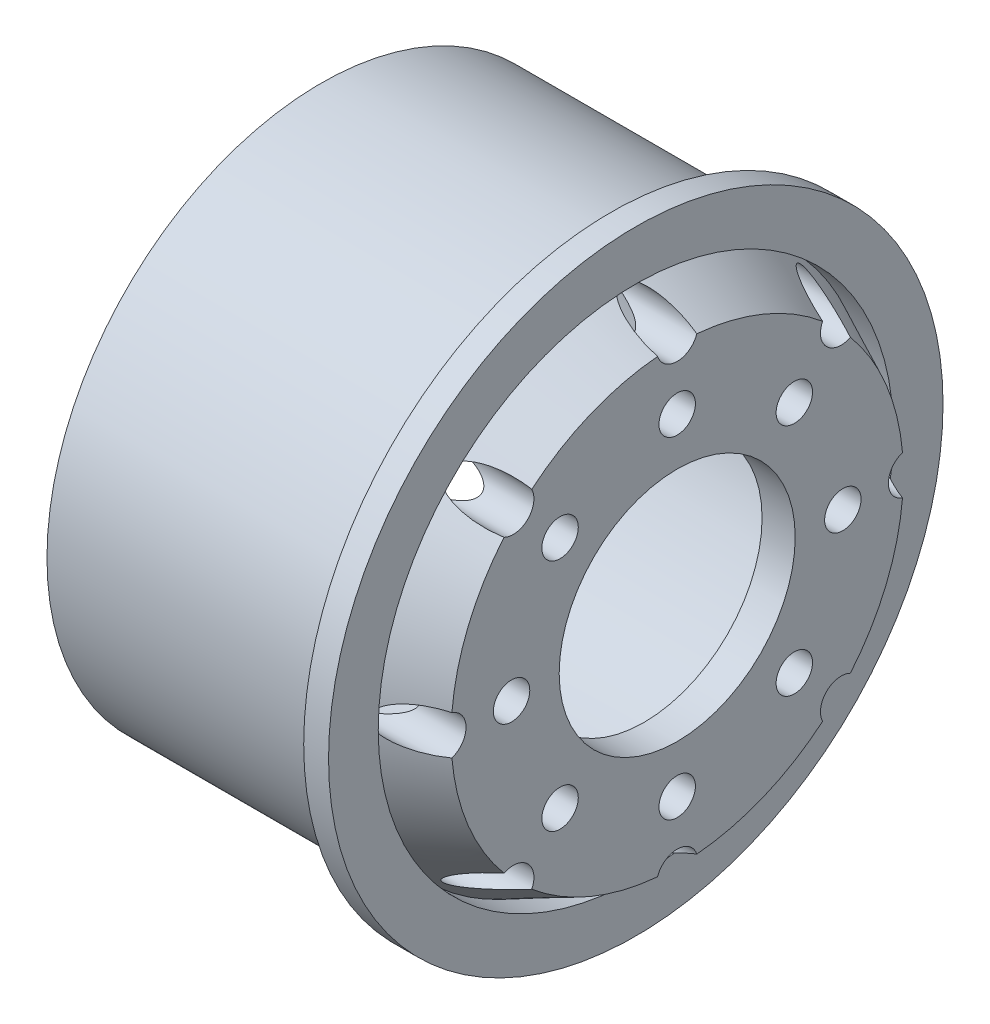
SolidWorks part; units mm, degrees
ref_plane "Front Plane" through (0, 0, 0) normal (0, 0, 1) x (1, 0, 0)
ref_plane "Top Plane" through (0, 0, 0) normal (0, 1, 0) x (1, 0, 0)
ref_plane "Right Plane" through (0, 0, 0) normal (1, 0, 0) x (0, 0, -1)
sketch "Sketch1" plane through (0, 0, 0) normal (0, 1, 0) x (1, 0, 0)
  line L0 (-37.2789, 0) -> (44.8184, 0) construction
  line L7 (8.9363, 7.125) -> (8.9363, 13.6543)
  line L11 (-12.5637, 14.55) -> (4.1816, 13.6944)
  line L12 (-12.5637, 14.55) -> (-12.5637, 16.55)
  line L13 (-12.5637, 16.55) -> (4.9363, 16.55)
  line L14 (6.4363, 16.55) -> (6.4363, 15.55)
  line L15 (6.4363, 16.55) -> (6.4363, 18.55)
  line L16 (6.4363, 18.55) -> (4.9363, 18.55)
  line L17 (4.9363, 18.55) -> (4.9363, 16.55)
  line L18 (6.4363, 15.55) -> (4.9363, 15.55)
  line L21 (6.9363, 12.3889) -> (6.9363, 7.125)
  line L22 (6.9363, 7.125) -> (8.9363, 7.125)
  line L23 (4.9363, 15.55) -> (8.9363, 13.6543)
  line L24 (4.1816, 13.6944) -> (6.9363, 12.3889)
  line L28 (4.0798, 13.7427) -> (8.0798, 11.847) construction
  point P4 (7.9363, 16.8502)
  dimension "D1" = 29.1
  dimension "D2" = 5.2639
  dimension "D4" = 2
  dimension "D5" = 16.7453
  dimension "D6" = 19
  dimension "D7" = 1.5
  dimension "D8" = 2
  dimension "D9" = 1.5
  dimension "D10" = 1
  dimension "D11" = 14.25
  dimension "D12" = 33.1
  dimension "D3" = 2
  dimension "D13" = 2.5
  dimension "D15" = 19.5
  dimension "D16" = 3.0484
  dimension "D17" = 27.3888
  dimension "D18" = 2.7547
  dimension "D19" = 24.7779
  dimension "D20" = 27.3888
  dimension "D21" = 1.3055
  dimension "D14" = 2
revolve "Revolve1" add sketch "Sketch1" angle 360 about L0
sketch "Sketch2" plane through (8.9363, 0, 0) normal (1, 0, 0) x (0, 0, -1)
  line L0 (0, 13.6543) -> (0, -13.6543) construction
  line L1 (-13.6543, 0) -> (13.6543, 0) construction
  circle A0 centre (0, 0) radius 13.6543 construction
  circle A1 centre (0, 0) radius 10 construction
  circle A2 centre (0, 10) radius 1.1
  circle A3 centre (7.0711, 7.0711) radius 1.1
  circle A4 centre (10, 0) radius 1.1
  circle A5 centre (7.0711, -7.0711) radius 1.1
  circle A6 centre (0, -10) radius 1.1
  circle A7 centre (-7.0711, -7.0711) radius 1.1
  circle A8 centre (-10, 0) radius 1.1
  circle A9 centre (-7.0711, 7.0711) radius 1.1
  circle A12 centre (0, 0) radius 14 construction
  circle A13 centre (0, -14) radius 1.25
  circle A14 centre (-9.8995, -9.8995) radius 1.25
  circle A15 centre (-14, 0) radius 1.25
  circle A16 centre (-9.8995, 9.8995) radius 1.25
  circle A17 centre (0, 14) radius 1.25
  circle A18 centre (9.8995, 9.8995) radius 1.25
  circle A19 centre (14, 0) radius 1.25
  circle A20 centre (9.8995, -9.8995) radius 1.25
  point P28 (0, 0)
  point P46 (0, 0)
  dimension "D1" = 20
  dimension "D2" = 2.2
  dimension "D4" = 28
  dimension "D5" = 2.5
  dimension "D3" = 8
  dimension "D6" = 8
extrude "Cut-Extrude1" cut sketch "Sketch2" against normal blind 5
